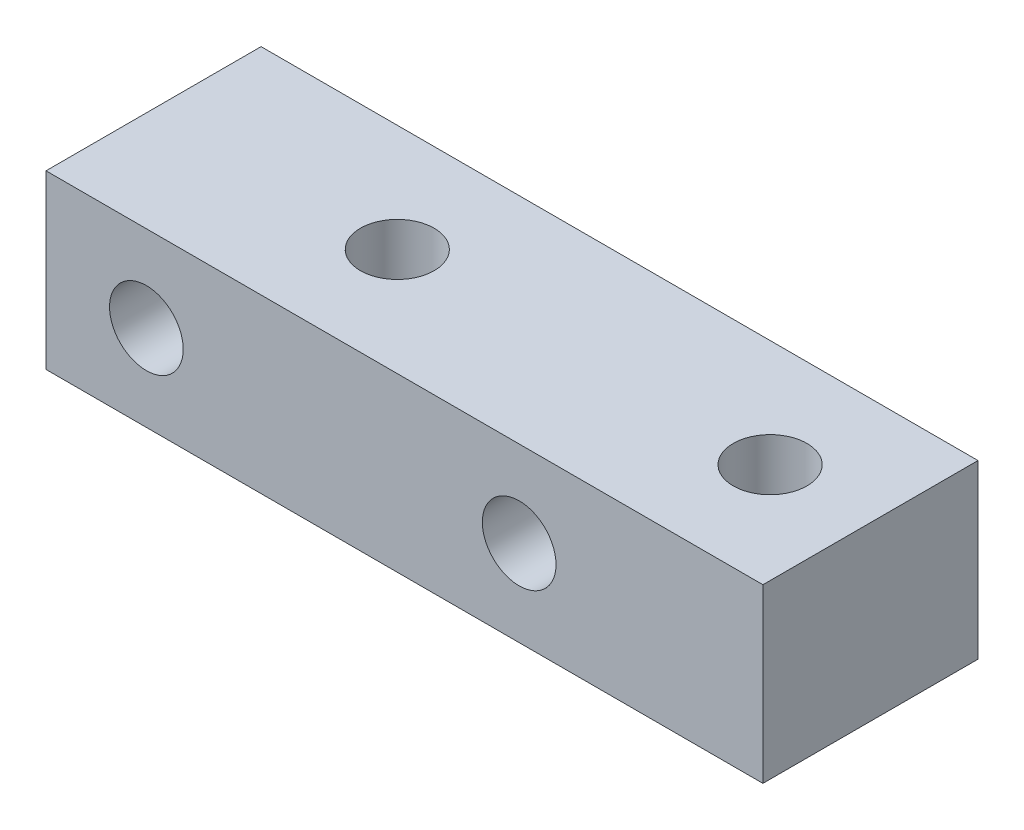
SolidWorks part; units mm, degrees
ref_plane "Front Plane" through (0, 0, 0) normal (0, 0, 1) x (1, 0, 0)
ref_plane "Top Plane" through (0, 0, 0) normal (0, 1, 0) x (1, 0, 0)
ref_plane "Right Plane" through (0, 0, 0) normal (1, 0, 0) x (0, 0, -1)
sketch "Sketch2" plane through (0, 0, 0) normal (0, 1, 0) x (1, 0, 0)
  line L1 (-31.75, 9.525) -> (31.75, 9.525)
  line L2 (-31.75, 9.525) -> (-31.75, -9.525)
  line L3 (-31.75, -9.525) -> (31.75, -9.525)
  line L4 (31.75, 9.525) -> (31.75, -9.525)
  line L5 (-31.75, 9.525) -> (31.75, -9.525) construction
  line L6 (-31.75, -9.525) -> (31.75, 9.525) construction
  point P0 (0, 0)
  dimension "D1" = 63.5
  dimension "D2" = 19.05
extrude "Boss-Extrude1" add sketch "Sketch2" against normal blind 15.24
sketch "Sketch4" plane through (0, 0, 0) normal (0, 1, 0) x (1, 0, 0)
  line L0 (0, 0) -> (0, 9.525) construction
  line L1 (31.75, 9.525) -> (-31.75, 9.525) construction
  line L2 (0, 0) -> (0, -9.525) construction
  line L3 (-31.75, -9.525) -> (31.75, -9.525) construction
  line L5 (-31.75, 9.525) -> (-31.75, -9.525) construction
  line L7 (0, 0) -> (-0.0377, 0) construction
  line L8 (0, 0) -> (-31.75, 0) construction
  line L9 (-0.0377, 0) -> (31.75, 0) construction
  line L10 (31.75, -9.525) -> (31.75, 9.525) construction
  circle A0 centre (-10.16, 0) radius 2.921
  circle A1 centre (22.86, 0) radius 2.921
  dimension "D2" = 5.842
  dimension "D3" = 5.842
  dimension "D1" = 33.02
  dimension "D4" = 8.89
sketch "Sketch5" plane through (0, 0, 9.525) normal (0, 0, 1) x (1, 0, 0)
  line L0 (0, 0) -> (0, -15.24) construction
  line L1 (-31.75, -15.24) -> (31.75, -15.24) construction
  line L2 (-31.75, -15.24) -> (-31.75, 0) construction
  line L3 (-31.75, 0) -> (31.75, 0) construction
  line L5 (0, -7.62) -> (31.75, -7.62) construction
  line L6 (31.75, -15.24) -> (31.75, 0) construction
  circle A0 centre (10.16, -7.62) radius 2.921
  circle A1 centre (-22.86, -7.62) radius 2.921
  dimension "D3" = 5.842
  dimension "D4" = 8.89
  dimension "0.23" = 5.842
  dimension "D1" = 33.02
  dimension "D2" = 7.62
  dimension "D5" = 7.62
hole_wizard "1/4 Clearance Hole2" positions "Sketch8" profile "Sketch9" hole size "1/4" standard "ANSI Inch" end condition through all
sketch "Sketch8" plane through (0, 0, 9.525) normal (0, 0, 1) x (1, 0, 0)
  point P0 (-22.86, -7.62)
  point P3 (10.16, -7.62)
sketch "Sketch9" plane through (-22.86, -7.62, 9.525) normal (1, 0, 0) x (0, -1, 0)
  line L0 (0, 0) -> (0, 19.05)
  line L1 (0, 19.05) -> (3.2639, 19.05)
  line L2 (3.2639, 19.05) -> (3.2639, 0)
  line L5 (3.2639, 0) -> (0, 0)
  line L11 (0, -6.35) -> (0, 107.95) construction
  dimension "Thru Hole Dia." = 6.5278
  dimension "Thru Hole Depth" = 19.05
hole_wizard "1/4 Clearance Hole3" positions "Sketch10" profile "Sketch11" hole size "1/4" standard "ANSI Inch" end condition through all
sketch "Sketch10" plane through (0, 0, 0) normal (0, 1, 0) x (1, 0, 0)
  point P0 (-10.16, 0)
  point P3 (22.86, 0)
sketch "Sketch11" plane through (-10.16, 0, 0) normal (1, 0, 0) x (0, 0, 1)
  line L0 (0, 0) -> (0, 15.24)
  line L1 (0, 15.24) -> (3.2639, 15.24)
  line L2 (3.2639, 15.24) -> (3.2639, 0)
  line L5 (3.2639, 0) -> (0, 0)
  line L11 (0, -6.35) -> (0, 107.95) construction
  dimension "Thru Hole Dia." = 6.5278
  dimension "Thru Hole Depth" = 15.24
